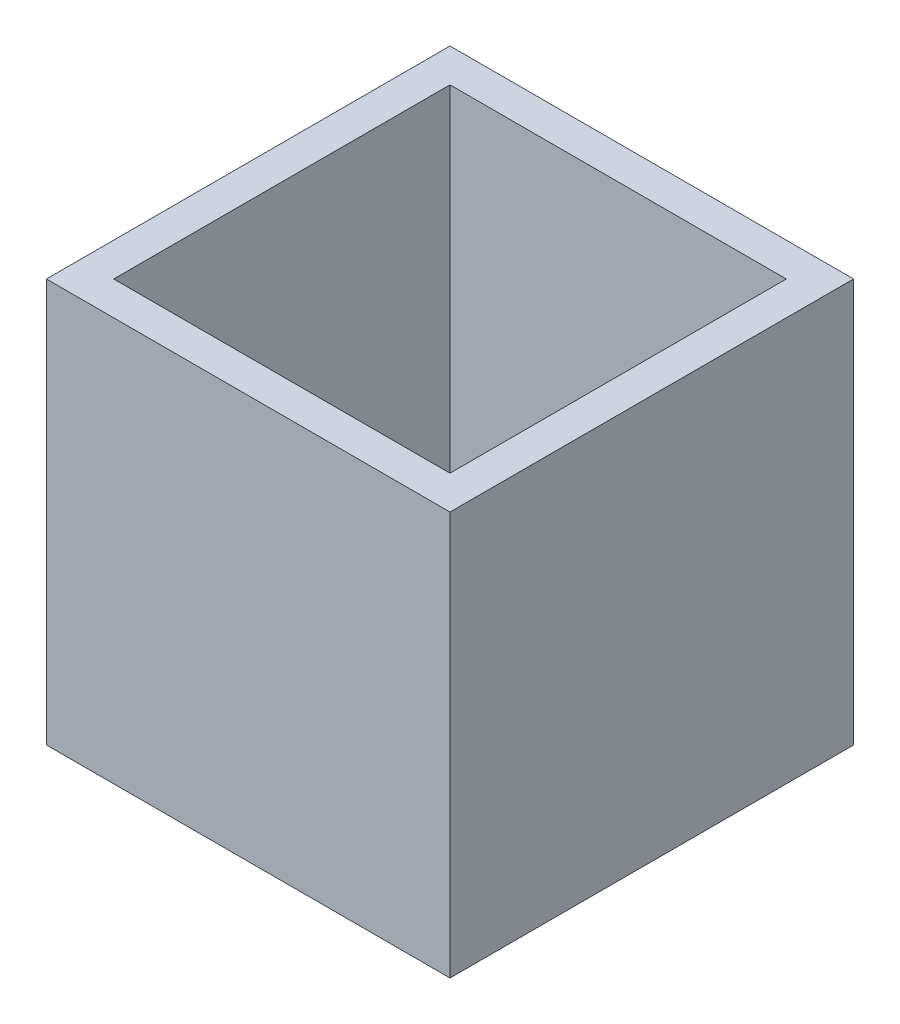
SolidWorks part; units mm, degrees
ref_plane "Front Plane" through (0, 0, 0) normal (0, 0, 1) x (1, 0, 0)
ref_plane "Top Plane" through (0, 0, 0) normal (0, 1, 0) x (1, 0, 0)
ref_plane "Right Plane" through (0, 0, 0) normal (1, 0, 0) x (0, 0, -1)
sketch "Sketch1" plane through (0, 0, 0) normal (0, 1, 0) x (1, 0, 0)
  line L1 (0, 12) -> (12, 12)
  line L2 (0, 12) -> (0, 0)
  line L3 (0, 0) -> (12, 0)
  line L4 (12, 12) -> (12, 0)
  dimension "D1" = 12
  dimension "D2" = 12
extrude "Boss-Extrude1" add sketch "Sketch1" along normal blind 12
sketch "Sketch2" plane through (0, 12, 0) normal (0, 1, 0) x (1, 0, 0)
  line L0 (12, 0) -> (12, 12) construction
  line L1 (11, 11) -> (1, 11)
  line L2 (11, 11) -> (11, 1)
  line L3 (11, 1) -> (1, 1)
  line L4 (1, 11) -> (1, 1)
  line L5 (0, 12) -> (0, 0) construction
  line L6 (0, 0) -> (12, 0) construction
  line L7 (12, 12) -> (0, 12) construction
  dimension "D1" = 1
  dimension "D2" = 1
  dimension "D3" = 1
  dimension "D4" = 1
extrude "Cut-Extrude1" cut sketch "Sketch2" against normal through all
